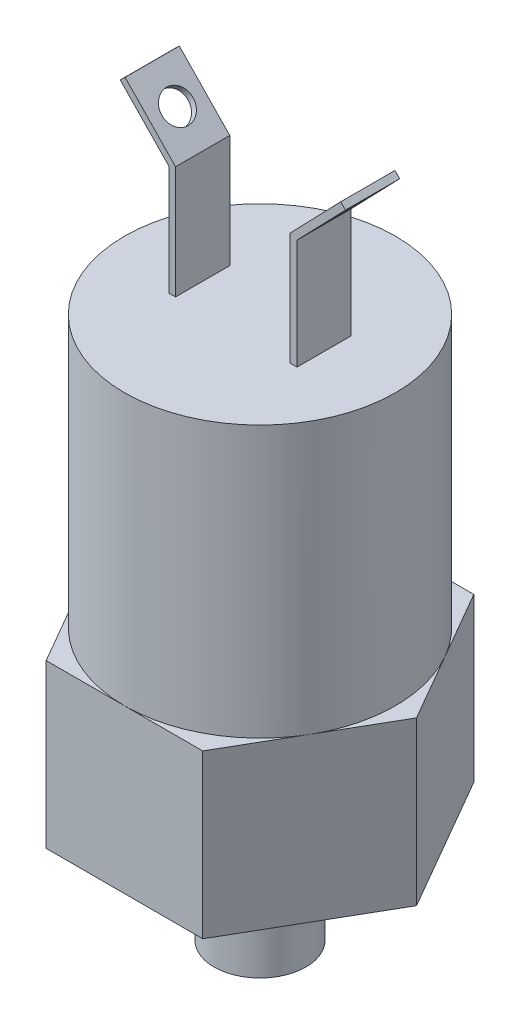
SolidWorks part; units mm, degrees
ref_plane "Front Plane" through (0, 0, 0) normal (0, 0, 1) x (1, 0, 0)
ref_plane "Top Plane" through (0, 0, 0) normal (0, 1, 0) x (1, 0, 0)
ref_plane "Right Plane" through (0, 0, 0) normal (1, 0, 0) x (0, 0, -1)
sketch "Sketch2" plane through (0, 0, 0) normal (0, 1, 0) x (1, 0, 0)
  line L0 (0, 0) -> (0, 12.7) construction
  line L1 (7.3323, 12.7) -> (-7.3323, 12.7)
  line L2 (-7.3323, 12.7) -> (-14.6647, 0)
  line L3 (-14.6647, 0) -> (-7.3323, -12.7)
  line L4 (-7.3323, -12.7) -> (7.3323, -12.7)
  line L5 (7.3323, -12.7) -> (14.6647, 0)
  line L6 (14.6647, 0) -> (7.3323, 12.7)
  circle A0 centre (0, 0) radius 12.7 construction
  dimension "D1" = 25.4
extrude "Boss-Extrude1" add sketch "Sketch2" along normal blind 15.24
sketch "Sketch3" plane through (0, 15.24, 0) normal (0, 1, 0) x (1, 0, 0)
  circle A0 centre (0, 0) radius 12.7
  dimension "D1" = 25.4
extrude "Boss-Extrude2" add sketch "Sketch3" along normal blind 25.4
sketch "Sketch4" plane through (0, 0, 0) normal (0, -1, 0) x (1, 0, 0)
  circle A0 centre (0, 0) radius 4.3053
  dimension "D1" = 8.6106
extrude "Boss-Extrude3" add sketch "Sketch4" along normal blind 10.16
cosmetic thread "Cosmetic Thread2" parameters "D2"=7.6106
sketch "Sketch5" plane through (0, 0, 0) normal (0, 0, 1) x (1, 0, 0)
  line L0 (5.6907, 40.64) -> (5.6907, 51.0752)
  line L1 (12.7, 40.64) -> (-12.7, 40.64) construction
  line L2 (5.6907, 51.0752) -> (10.3268, 55.88)
  dimension "D1" = 15.24
extrude "Extrude-Thin1" add sketch "Sketch5" along normal mid plane 5.08 thin thin type mid plane wall 0.635
sketch "Sketch6" plane through (-22.8028, 22.0022, 0) normal (-0.7196, 0.6944, 0) x (0, 0, 1)
  line L1 (2.54, 47.3833) -> (-2.54, 47.3833) construction
  line L2 (0, 43.9808) -> (0, 47.3833) construction
  line L3 (0, 43.9808) -> (-2.54, 43.9808) construction
  line L4 (-2.54, 40.5783) -> (-2.54, 47.3833) construction
  circle A0 centre (0, 43.9808) radius 1.4605
  dimension "D1" = 2.921
extrude "Cut-Extrude1" cut sketch "Sketch6" against normal up to next (0.635 mm away)
mirror "Mirror1" about plane through (0, 0, 0) normal (1, 0, 0) of "Extrude-Thin1", "Cut-Extrude1"
